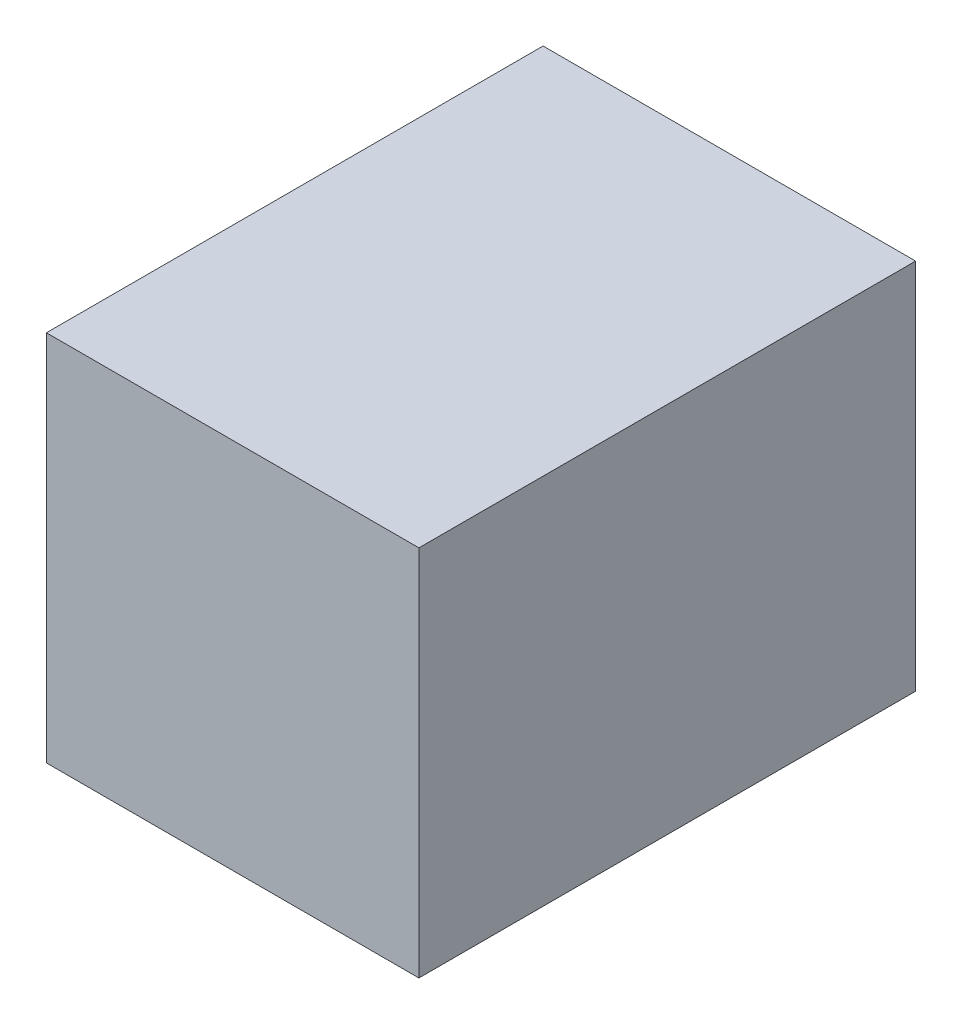
SolidWorks part; units mm, degrees
ref_plane "Front Plane" through (0, 0, 0) normal (0, 0, 1) x (1, 0, 0)
ref_plane "Top Plane" through (0, 0, 0) normal (0, 1, 0) x (1, 0, 0)
ref_plane "Right Plane" through (0, 0, 0) normal (1, 0, 0) x (0, 0, -1)
sketch "Sketch1" plane through (0, 0, 0) normal (0, 0, 1) x (1, 0, 0)
  line L1 (-3, -3) -> (3, -3)
  line L2 (-3, -3) -> (-3, 3)
  line L3 (-3, 3) -> (3, 3)
  line L4 (3, -3) -> (3, 3)
  line L5 (-3, -3) -> (3, 3) construction
  line L6 (-3, 3) -> (3, -3) construction
  point P0 (0, 0)
  dimension "D1" = 6
  dimension "D2" = 6
extrude "Boss-Extrude1" add sketch "Sketch1" along normal blind 8
